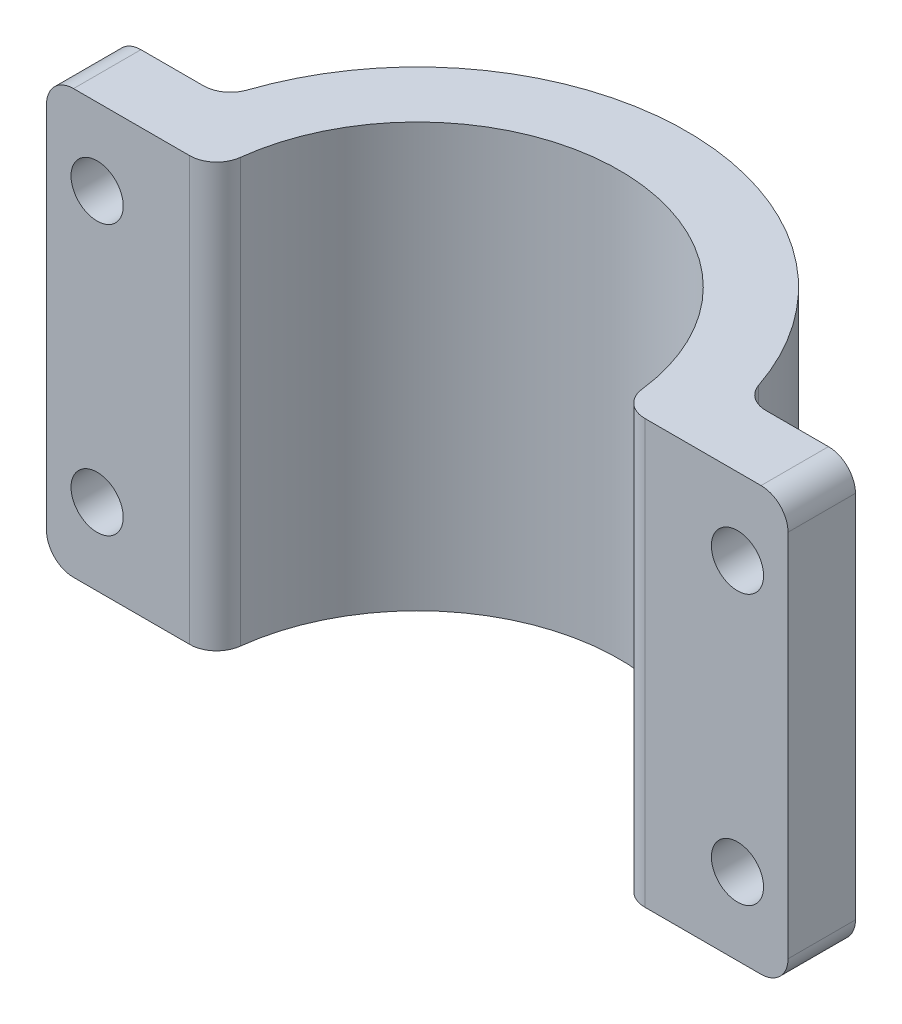
SolidWorks part; units mm, degrees
material "6061-T6 (SS)"
ref_plane "Front Plane" through (0, 0, 0) normal (0, 0, 1) x (1, 0, 0)
ref_plane "Top Plane" through (0, 0, 0) normal (0, 1, 0) x (1, 0, 0)
ref_plane "Right Plane" through (0, 0, 0) normal (1, 0, 0) x (0, 0, -1)
sketch "Sketch5" plane through (0, 0, 0) normal (0, 1, 0) x (1, 0, 0)
  line L0 (-34.925, 0) -> (-19.05, 0)
  line L1 (19.05, 0) -> (34.925, 0)
  line L2 (-34.925, 0) -> (-34.925, 6.35)
  line L3 (-34.925, 6.35) -> (-24.5934, 6.35)
  line L4 (34.925, 0) -> (34.925, 6.35)
  line L5 (34.925, 6.35) -> (24.5934, 6.35)
  arc A0 (19.05, 0) -> (-19.05, 0) centre (0, 0) ccw
  arc A1 (24.5934, 6.35) -> (-24.5934, 6.35) centre (0, 0) ccw
  dimension "D2" = 19.05
  dimension "D4" = 6.35
  dimension "D1" = 6.35
  dimension "D3" = 15.875
extrude "Boss-Extrude2" add sketch "Sketch5" against normal blind 39.878
fillet "Fillet1" radius 2.54 8 edges at (19.05, -19.939, 0) (24.5934, -19.939, -6.35) (-24.5934, -19.939, -6.35) (-19.05, -19.939, 0) (-34.925, 0, -3.175) (-34.925, -39.878, -3.175) (34.925, -39.878, -3.175) (34.925, 0, -3.175)
hole_wizard "#10 (0.1935) Diameter Hole1" positions "Sketch6" profile "Sketch7" hole size "#10" standard "ANSI Inch" end condition through all
sketch "Sketch6" plane through (0, 0, -6.35) normal (0, 0, -1) x (-1, 0, 0)
  line L0 (-30.1625, -7.239) -> (-30.1625, -32.639) construction
  line L2 (-30.1625, -19.939) -> (-34.925, -19.939) construction
  line L3 (-34.925, -37.338) -> (-34.925, -2.54) construction
  point P0 (-30.1625, -7.239)
  point P2 (-30.1625, -32.639)
  dimension "D1" = 25.4
  dimension "D2" = 4.7625
sketch "Sketch7" plane through (30.1625, -7.239, -6.35) normal (1, 0, 0) x (0, 1, 0)
  line L0 (0, 0) -> (0, 6.35)
  line L1 (0, 6.35) -> (2.4574, 6.35)
  line L2 (2.4574, 6.35) -> (2.4574, 0)
  line L5 (2.4574, 0) -> (0, 0)
  line L11 (0, -6.35) -> (0, 107.95) construction
  dimension "Thru Hole Dia." = 4.9149
  dimension "Thru Hole Depth" = 6.35
mirror "Mirror1" about plane through (0, 0, 0) normal (1, 0, 0) of "#10 (0.1935) Diameter Hole1"
